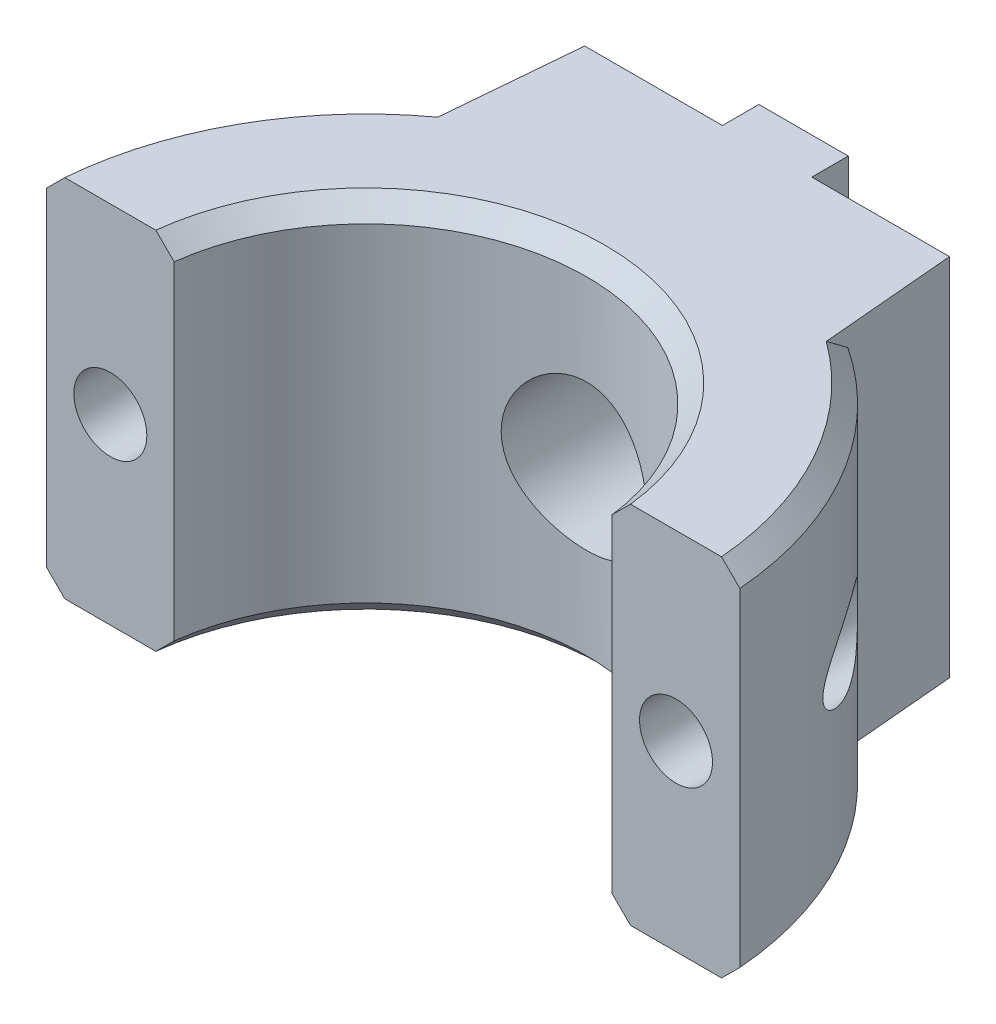
SolidWorks part; units mm, degrees
material "PUR"
ref_plane "Ebene vorne" through (0, 0, 0) normal (0, 0, 1) x (1, 0, 0)
ref_plane "Ebene oben" through (0, 0, 0) normal (0, 1, 0) x (1, 0, 0)
ref_plane "Ebene rechts" through (0, 0, 0) normal (1, 0, 0) x (0, 0, -1)
sketch "Skizze1" plane through (0, 0, 0) normal (0, 1, 0) x (1, 0, 0)
  line L0 (0, 0) -> (-28.074, 0) construction
  line L1 (-19.0067, 1.5) -> (-12.0067, 1.5)
  line L2 (19.0067, 1.5) -> (12.0067, 1.5)
  line L3 (-10, 22) -> (10, 22)
  line L4 (-10, 22) -> (-10.5345, 15.8911)
  line L5 (10, 22) -> (10.5345, 15.8911)
  circle A0 centre (0, 0) radius 12.1
  arc A1 (-19.0067, 1.5) -> (-10.5345, 15.8911) centre (0, 0) cw
  arc A2 (10.5345, 15.8911) -> (19.0067, 1.5) centre (0, 0) cw
  point P10 (0, 22)
  dimension "D1" = 24.2
  dimension "D2" = 1.5
  dimension "D3" = 7
  dimension "D4" = 20
  dimension "D5" = 22
  dimension "D6" = 10
extrude "Aufsatz-Linear austragen1" add sketch "Skizze1" along normal mid plane 20 contours A2 L5 L3 L4 A1 L1 A0 L2
sketch "Skizze4" plane through (0, 0, -22) normal (0, 0, -1) x (-1, 0, 0)
  line L0 (10, 10) -> (-10, 10) construction
  line L1 (2.45, -10) -> (-2.45, -10)
  line L2 (2.45, -10) -> (2.45, 10)
  line L3 (2.45, 10) -> (-2.45, 10)
  line L4 (-2.45, -10) -> (-2.45, 10)
  line L5 (2.45, -10) -> (-2.45, 10) construction
  line L6 (2.45, 10) -> (-2.45, -10) construction
  point P0 (0, 0)
  dimension "D1" = 4.9
extrude "Aufsatz-Linear austragen2" add sketch "Skizze4" along normal blind 2
hole_wizard "Stirnsenkung für M4 Zylinderschraube mit Innensechskant1" positions "Skizze2" profile "Skizze3" counterbore size "M4" standard "ISO" end condition through all
sketch "Skizze2" plane through (0, 0, -1.5) normal (0, 0, 1) x (1, 0, 0)
  point P0 (0, 0)
sketch "Skizze3" plane through (0, 0, -1.5) normal (1, 0, 0) x (0, -1, 0)
  line L0 (0, 0) -> (0, 22.5)
  line L1 (0, 22.5) -> (2.25, 22.5)
  line L3 (2.25, 22.5) -> (2.25, 16)
  line L4 (2.25, 16) -> (4, 16)
  line L5 (4, 16) -> (4, 0)
  line L7 (4, 0) -> (0, 0)
  line L11 (0, -6.35) -> (0, 107.95) construction
  dimension "Bohrerdurchmesser" = 4.5
  dimension "Bohrungstiefe" = 22.5
  dimension "Senkdurchmesser2" = 8
  dimension "Senktiefe2" = 16
hole_wizard "Ø4.0 (4) Durchmesser Bohrung1" positions "Skizze5" profile "Skizze6" hole size "Ø4.0" standard "ISO" end condition through all
sketch "Skizze5" plane through (0, 0, -1.5) normal (0, 0, 1) x (1, 0, 0)
  line L0 (15.5067, 10) -> (15.5067, 0) construction
  line L1 (19.0067, 10) -> (12.0067, 10) construction
  line L2 (15.5067, 0) -> (0, 0) construction
  line L3 (0, 0) -> (-15.5067, 0) construction
  line L4 (-15.5067, 0) -> (-15.5067, 10) construction
  line L5 (-19.0067, 10) -> (-12.0067, 10) construction
  point P0 (-15.5067, 0)
  point P2 (15.5067, 0)
sketch "Skizze6" plane through (-15.5067, 0, -1.5) normal (1, 0, 0) x (0, -1, 0)
  line L0 (0, 0) -> (0, 22.5)
  line L1 (0, 22.5) -> (2, 22.5)
  line L2 (2, 22.5) -> (2, 0)
  line L5 (2, 0) -> (0, 0)
  line L11 (0, -6.35) -> (0, 107.95) construction
  dimension "Bohrerdurchmesser" = 4
  dimension "Bohrungstiefe" = 22.5
chamfer "Fase1" distance 1 angle 45 6 edges at (16.43, -10, -9.6725) (-16.43, -10, -9.6725) (16.43, 10, -9.6725) (-16.43, 10, -9.6725) (0, -10, -12.1) (0, 10, -12.1)
